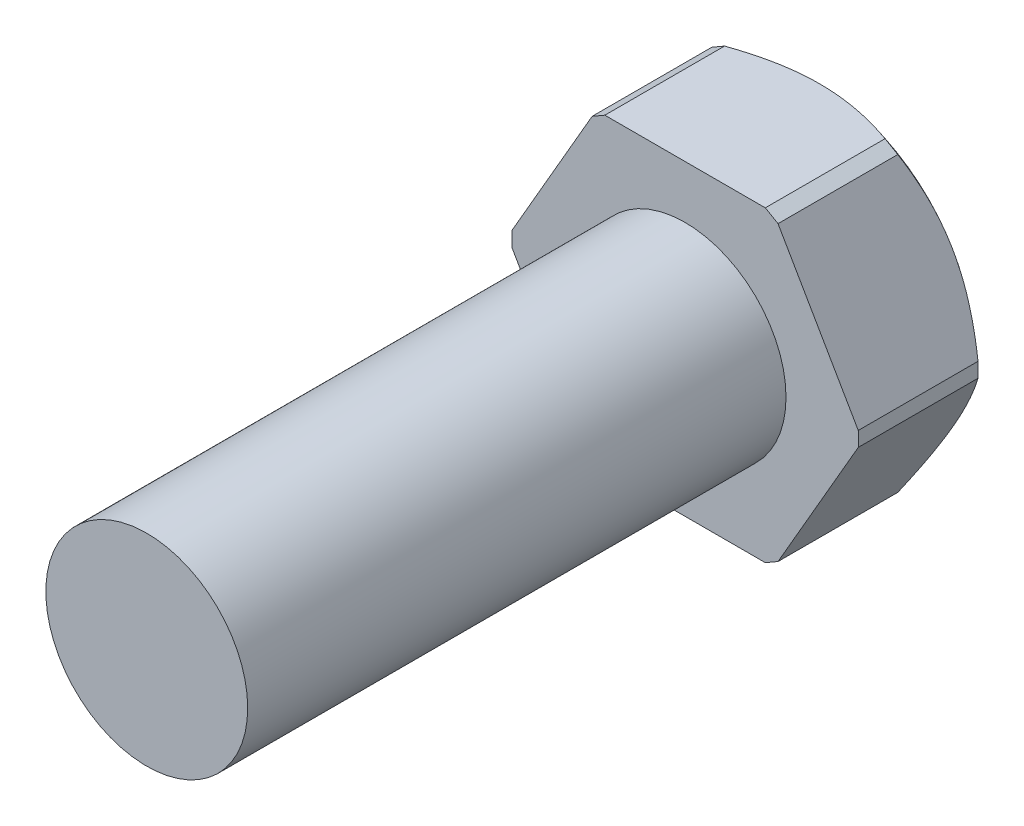
SolidWorks part; units mm, degrees
ref_plane "Alzado" through (0, 0, 0) normal (0, 0, 1) x (1, 0, 0)
ref_plane "Planta" through (0, 0, 0) normal (0, 1, 0) x (1, 0, 0)
ref_plane "Vista lateral" through (0, 0, 0) normal (1, 0, 0) x (0, 0, -1)
sketch "Croquis1" plane through (0, 0, 0) normal (0, 0, 1) x (1, 0, 0)
  line L1 (8.3716, 0) -> (4.1858, 7.25)
  line L2 (4.1858, 7.25) -> (-4.1858, 7.25)
  line L3 (-4.1858, 7.25) -> (-8.3716, 0)
  line L4 (-8.3716, 0) -> (-4.1858, -7.25)
  line L5 (-4.1858, -7.25) -> (4.1858, -7.25)
  line L6 (4.1858, -7.25) -> (8.3716, 0)
  circle A0 centre (0, 0) radius 7.25 construction
  dimension "D1" = 14.5
extrude "Saliente-Extruir1" add sketch "Croquis1" along normal blind 6.35
sketch "Croquis2" plane through (0, 0, 6.35) normal (0, 0, 1) x (1, 0, 0)
  circle A0 centre (0, 0) radius 4.7625
  dimension "D1" = 9.525
extrude "Saliente-Extruir2" add sketch "Croquis2" along normal blind 25.4
sketch "Croquis3" plane through (0, 0, 0) normal (0, 0, -1) x (-1, 0, 0)
  circle A0 centre (0, 0) radius 7.25
  circle A1 centre (0, 0) radius 33.7186
extrude "Cortar-Extruir1" cut sketch "Croquis3" against normal blind 76.2 draft 53
sketch "Croquis4" plane through (0, 0, 0) normal (0, 0, -1) x (-1, 0, 0)
  line L0 (0, 0) -> (-4.1858, 7.25) construction
  line L1 (-4.0858, 7.0768) -> (-3.3107, 7.5243)
  line L2 (-3.3107, 7.5243) -> (-3.6185, 8.0575)
  line L3 (-4.0858, 7.0768) -> (-4.9344, 6.5868)
  line L4 (-4.9344, 6.5868) -> (-5.2423, 7.12)
  line L5 (-3.6185, 8.0575) -> (-5.2423, 7.12)
  dimension "D1" = 0.2
extrude "Cortar-Extruir2" cut sketch "Croquis4" against normal blind 10
pattern_circular "MatrizC1" count 6 every 60 about axis through (0, 0, 0) along (0, 0, 1) of "Cortar-Extruir2"
